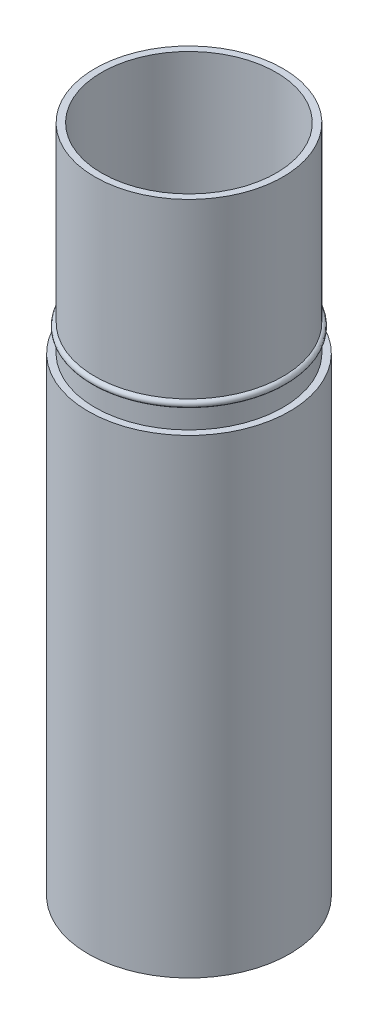
SolidWorks part; units mm, degrees
ref_plane "Front Plane" through (0, 0, 0) normal (0, 0, 1) x (1, 0, 0)
ref_plane "Top Plane" through (0, 0, 0) normal (0, 1, 0) x (1, 0, 0)
ref_plane "Right Plane" through (0, 0, 0) normal (1, 0, 0) x (0, 0, -1)
sketch "Sketch1" plane through (0, 0, 0) normal (0, 1, 0) x (1, 0, 0)
  circle A0 centre (0, 0) radius 15
  dimension "D1" = 30
extrude "Boss-Extrude1" add sketch "Sketch1" along normal blind 70
sketch "Sketch2" plane through (0, 70, 0) normal (0, 1, 0) x (1, 0, 0)
  circle A0 centre (0, 0) radius 14
  dimension "D1" = 28
extrude "Boss-Extrude2" add sketch "Sketch2" along normal blind 16
sketch "Sketch3" plane through (0, 0, 0) normal (0, 0, 1) x (1, 0, 0)
  line L0 (-14, 86) -> (-14, 70) construction
  line L3 (15, 70) -> (-15, 70) construction
  line L4 (0, 70) -> (0, 86) construction
  line L5 (14, 86) -> (-14, 86) construction
  circle A0 centre (-14, 73.5) radius 0.5
  dimension "D2" = 1
  dimension "D1" = 3.5
revolve "Revolve1" add sketch "Sketch3" angle 360 about L4
sketch "Sketch4" plane through (0, 86, 0) normal (0, 1, 0) x (1, 0, 0)
  circle A0 centre (0, 0) radius 13
  dimension "D1" = 26
extrude "Cut-Extrude1" cut sketch "Sketch4" against normal blind 78
sketch "Sketch5" plane through (0, 8, 0) normal (0, 1, 0) x (1, 0, 0)
  circle A0 centre (0, 0) radius 2
  dimension "D1" = 4
extrude "Cut-Extrude2" cut sketch "Sketch5" against normal through all
sketch "Sketch6" plane through (0, 8, 0) normal (0, 1, 0) x (1, 0, 0)
  line L1 (-0.5, 12.5) -> (0.5, 12.5)
  line L2 (-0.5, 12.5) -> (-0.5, 13.292)
  line L3 (-0.5, 13.292) -> (0.5, 13.292)
  line L4 (0.5, 12.5) -> (0.5, 13.292)
  circle A0 centre (0, 0) radius 13 construction
  dimension "D1" = 0.5
  dimension "D2" = 1
  dimension "D3" = 12.5
extrude "Boss-Extrude3" add sketch "Sketch6" along normal blind 75
pattern_circular "CirPattern1" count 3 over 360 about axis through (0, 0, 0) along (0, 1, 0) of "Boss-Extrude3"
sketch "Sketch7" plane through (0, 0, 0) normal (0, -1, 0) x (1, 0, 0)
  circle A0 centre (0, 0) radius 14
  dimension "D1" = 28
extrude "Cut-Extrude3" cut sketch "Sketch7" against normal blind 5
scale "Scale1" scale about origin uniform scaling yes scale factor 0.655
sketch "Sketch8" plane through (0, 56.33, 0) normal (0, 1, 0) x (1, 0, 0)
  circle A0 centre (0, 0) radius 9.17
  circle A1 centre (0, 0) radius 8.515
extrude "Boss-Extrude4" add sketch "Sketch8" along normal blind 9
